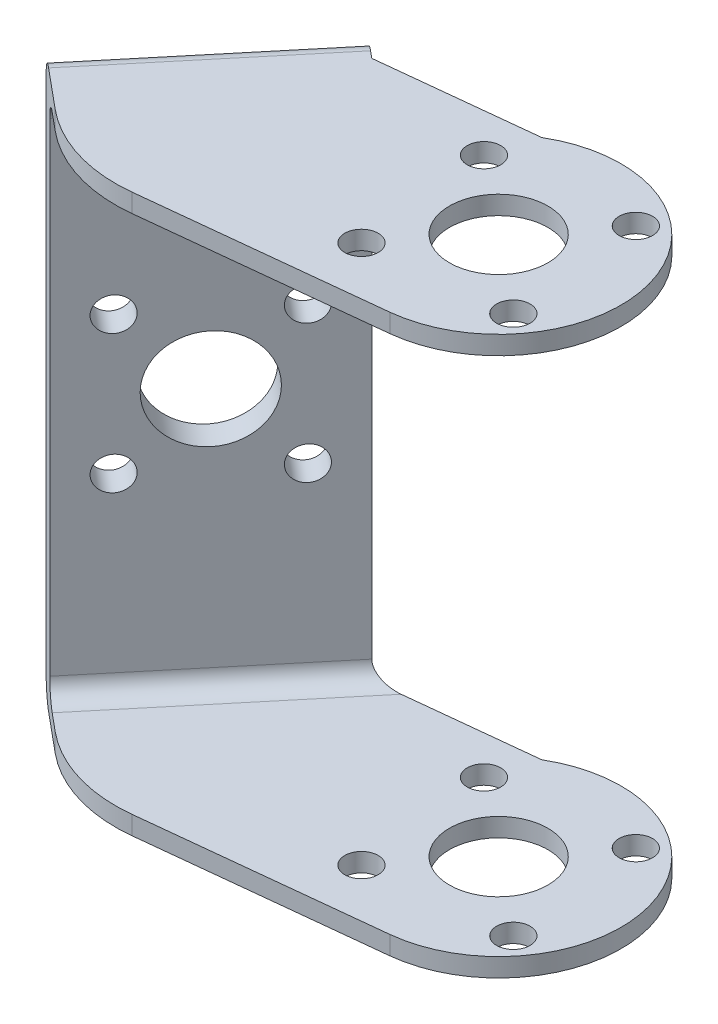
SolidWorks part; units mm, degrees
ref_plane "Alzado" through (0, 0, 0) normal (0, 0, 1) x (1, 0, 0)
ref_plane "Planta" through (0, 0, 0) normal (0, 1, 0) x (1, 0, 0)
ref_plane "Vista lateral" through (0, 0, 0) normal (1, 0, 0) x (0, 0, -1)
sketch "Croquis1" plane through (0, 0, 0) normal (0, 1, 0) x (1, 0, 0)
  line L0 (-10.995, -15.7898) -> (14.0877, -13.1051)
  line L1 (-10.5537, 9.5812) -> (5.9879, 11.3517)
  line L2 (-22.8373, -12.2109) -> (-26.2873, -9.3425)
  line L3 (-10.5537, 9.5812) -> (-26.2873, -9.3425)
  line L4 (-12.685, 0) -> (12.685, 0) construction
  arc A0 (14.0877, -13.1051) -> (5.9879, 11.3517) centre (12.685, 0) ccw
  arc A1 (-22.8373, -12.2109) -> (-10.995, -15.7898) centre (-12.685, 0) ccw
  circle A2 centre (12.685, 0) radius 5.3
  dimension "D1" = 26.36
  dimension "D2" = 31.76
  dimension "D7" = 10.6
  dimension "D3" = 25.18
  dimension "D4" = 134.15
  dimension "D5" = 25.37
  dimension "D6" = 24.61
extrude "Saliente-Extruir1" add sketch "Croquis1" along normal blind 2
sketch "Croquis2" plane through (0, 2, 0) normal (0, 1, 0) x (1, 0, 0)
  line L0 (-10.995, -15.7898) -> (14.0877, -13.1051) construction
  line L1 (4.5124, 6.5923) -> (19.2773, 8.1726) construction
  line L2 (4.5124, 6.5923) -> (6.0927, -8.1726) construction
  line L3 (6.0927, -8.1726) -> (20.8576, -6.5923) construction
  line L4 (19.2773, 8.1726) -> (20.8576, -6.5923) construction
  line L5 (4.5124, 6.5923) -> (20.8576, -6.5923) construction
  line L6 (6.0927, -8.1726) -> (19.2773, 8.1726) construction
  circle A0 centre (12.685, 0) radius 10.5 construction
  circle A1 centre (6.0927, -8.1726) radius 1.8
  circle A2 centre (20.8576, -6.5923) radius 1.8
  circle A3 centre (19.2773, 8.1726) radius 1.8
  circle A4 centre (4.5124, 6.5923) radius 1.8
  dimension "D1" = 21
  dimension "D2" = 3.6
extrude "Cortar-Extruir1" cut sketch "Croquis2" against normal blind 2
sketch "Croquis3" plane through (-10.9503, 0, -9.1043) normal (-0.7689, 0, -0.6393) x (-0.6393, 0, 0.7689)
  line L1 (-0.6203, 0) -> (23.9897, 0)
  line L2 (-0.6203, 0) -> (-0.6203, 60)
  line L3 (-0.6203, 60) -> (23.9897, 60)
  line L4 (23.9897, 0) -> (23.9897, 60)
  dimension "D1" = 60
extrude "Saliente-Extruir2" add sketch "Croquis3" along normal blind 2
sketch "Croquis4" plane through (0, 60, 0) normal (0, 1, 0) x (1, 0, 0)
  line L0 (14.0877, -13.1051) -> (-10.995, -15.7898)
  line L1 (-10.995, -15.7898) -> (14.0877, -13.1051) construction
  line L2 (-10.5537, 9.5812) -> (5.9879, 11.3517)
  line L3 (5.9879, 11.3517) -> (-10.5537, 9.5812) construction
  line L4 (-10.5537, 9.5812) -> (-26.2873, -9.3425)
  line L5 (-26.2873, -9.3425) -> (-22.8373, -12.2109)
  line L6 (-26.2873, -9.3425) -> (-10.5537, 9.5812) construction
  circle A0 centre (12.685, 0) radius 5.3
  arc A1 (14.0877, -13.1051) -> (5.9879, 11.3517) centre (12.685, 0) ccw
  arc A2 (14.0877, -13.1051) -> (5.9879, 11.3517) centre (12.685, 0) ccw construction
  circle A3 centre (12.685, 0) radius 5.3 construction
  arc A4 (-22.8373, -12.2109) -> (-10.995, -15.7898) centre (-12.685, 0) ccw
  arc A5 (-22.8373, -12.2109) -> (-10.995, -15.7898) centre (-12.685, 0) ccw construction
  circle A6 centre (4.5124, 6.5923) radius 1.8
  circle A7 centre (19.2773, 8.1726) radius 1.8
  circle A8 centre (20.8576, -6.5923) radius 1.8
  circle A9 centre (6.0927, -8.1726) radius 1.8
  circle A10 centre (19.2773, 8.1726) radius 1.8 construction
  circle A11 centre (4.5124, 6.5923) radius 1.8 construction
  circle A12 centre (6.0927, -8.1726) radius 1.8 construction
  circle A13 centre (20.8576, -6.5923) radius 1.8 construction
extrude "Saliente-Extruir3" add sketch "Croquis4" against normal blind 2
sketch "Croquis6" plane through (-12.4882, 0, -10.3829) normal (0.7689, 0, 0.6393) x (0.6393, 0, -0.7689)
  line L1 (0.6203, 0) -> (-23.9897, 0)
  line L2 (0.6203, 0) -> (0.6203, 60)
  line L3 (0.6203, 60) -> (-23.9897, 60)
  line L4 (-23.9897, 0) -> (-23.9897, 60)
  line L5 (-23.9897, 2) -> (-23.9897, 58) construction
  line L7 (0.6203, 0) -> (-23.9897, 0) construction
sketch "Croquis5" plane through (-12.4882, 0, -10.3829) normal (-0.7689, 0, -0.6393) x (-0.6393, 0, 0.7689)
  line L0 (11.6847, 0) -> (11.6847, 60) construction
  line L1 (-0.6203, 0) -> (23.9897, 0) construction
  line L2 (23.9897, 60) -> (-0.6203, 60) construction
  line L3 (-0.6203, 30) -> (23.9897, 30) construction
  line L4 (-0.6203, 60) -> (-0.6203, 0) construction
  line L5 (23.9897, 0) -> (23.9897, 60) construction
  line L7 (4.2601, 22.5754) -> (19.1093, 37.4246) construction
  circle A0 centre (11.6847, 30) radius 5.4
  circle A1 centre (11.6847, 30) radius 10.5 construction
  circle A2 centre (19.1093, 37.4246) radius 1.8
  circle A3 centre (11.6847, 30) radius 10.5 construction
  circle A4 centre (19.1093, 22.5754) radius 1.8
  circle A5 centre (11.6847, 30) radius 10.5 construction
  circle A6 centre (4.2601, 22.5754) radius 1.8
  circle A7 centre (11.6847, 30) radius 10.5 construction
  circle A8 centre (4.2601, 37.4246) radius 1.8
  point P29 (11.6847, 30)
  dimension "D2" = 3.6
  dimension "D3" = 21
  dimension "D4" = 10.8
  dimension "D5" = 45
  dimension "D1" = 4
extrude "Cortar-Extruir2" cut sketch "Croquis5" against normal up to next
extrude "Saliente-Extruir4" add sketch "Croquis6" against normal blind 1
sketch "Croquis7" plane through (-13.2571, 0, -11.0222) normal (-0.7689, 0, -0.6393) x (-0.6393, 0, 0.7689)
  circle A0 centre (11.6847, 30) radius 5.4
  circle A1 centre (11.6847, 30) radius 5.4 construction
  circle A2 centre (4.2601, 37.4246) radius 1.8
  circle A3 centre (19.1093, 37.4246) radius 1.8
  circle A4 centre (19.1093, 22.5754) radius 1.8
  circle A5 centre (4.2601, 22.5754) radius 1.8
  circle A6 centre (19.1093, 22.5754) radius 1.8 construction
  circle A7 centre (4.2601, 22.5754) radius 1.8 construction
  circle A8 centre (4.2601, 37.4246) radius 1.8 construction
  circle A9 centre (19.1093, 37.4246) radius 1.8 construction
extrude "Cortar-Extruir3" cut sketch "Croquis7" against normal up to next
fillet "Redondeo1" radius 2 4 edges at (-20.7273, 0, -2.0373) (-20.7273, 60, -2.0373) (-18.4205, 58, -0.1194) (-18.4205, 2, -0.1194)
